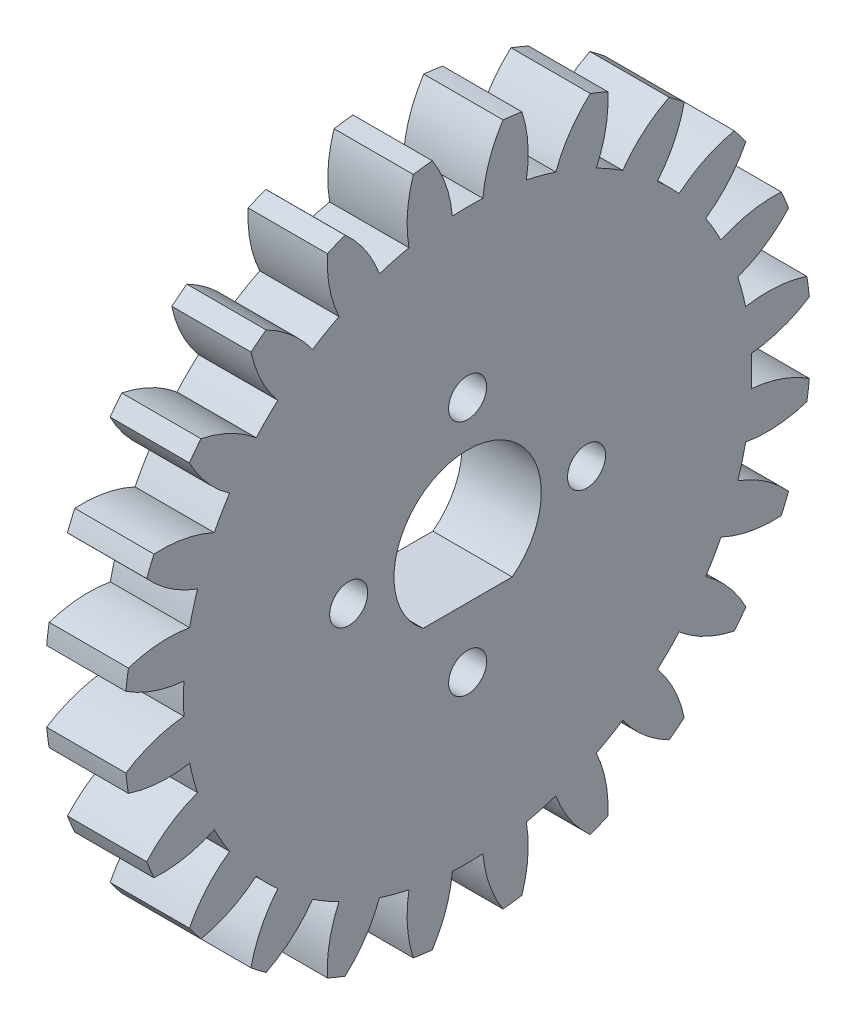
SolidWorks part; units mm, degrees
ref_plane "Plane1" through (0, 0, 0) normal (0, 0, 1) x (1, 0, 0)
ref_plane "Plane2" through (0, 0, 0) normal (0, 1, 0) x (1, 0, 0)
ref_plane "Plane3" through (0, 0, 0) normal (1, 0, 0) x (0, 0, -1)
sketch "HoldingSke" plane through (0, 0, 0) normal (0, 1, 0) x (1, 0, 0)
  line L0 (0, 0) -> (556.8973, -247.9467)
  line L1 (-15, 0) -> (100, 0) construction
  line L2 (0, 0) -> (-2.1039, 2.3779)
  line L3 (0, 0) -> (-11.863, 4.5341)
  line L4 (0, 0) -> (7.8894, 3.5126)
  line L5 (0, 0) -> (-47.5972, -17.7524)
  line L6 (0, 0) -> (-2.632, -1.7758)
  line L7 (-2.1039, 2.3779) -> (8.8315, 51.9902)
  line L8 (-76.2, 54.61) -> (-71.1708, 54.61)
  line L9 (-67.7845, 28.3722) -> (-49.3413, 33.142)
  line L10 (-76.2, 71.12) -> (104.1128, 71.12)
  line L11 (0, 0) -> (-3.175, 0)
  line L12 (-76.2, 101.6) -> (-76.1573, 101.6)
  line L13 (24.9733, 27.94) -> (52.9518, 28.4284)
  line L14 (24.9733, 27.94) -> (25.0241, 27.9398)
  line L15 (24.9733, 27.94) -> (100.4021, 29.52)
  circle A0 centre (0, 0) radius 2.3813
  circle A1 centre (0, 0) radius 10.3209
  circle A2 centre (0, 0) radius 38.1
  circle A3 centre (0, 0) radius 2.3813
  dimension "MHD" = 20.6417
  dimension "Hub_dia" = 76.2
  dimension "Bore" = 4.7625
  dimension "MBD" = 4.7625
  dimension "Num_teeth" = 24
  dimension "Pitch_radius" = 180.3128
  dimension "Pitch" = 609.6
  dimension "Width" = 3.175
  dimension "Overall_len" = 50.8
  dimension "Show_teeth" = 24
  dimension "Thickness" = 3.175
  dimension "OAL" = 50.8032
  dimension "T_dim" = 5.0292
  dimension "Ap" = 14.5
  dimension "H" = 19.05
  dimension "Backlash" = 0.0427
  dimension "Addendum_fac" = 1
  dimension "Dedendum_fac" = 1.2
  dimension "Clearance_fac" = 0.2
  dimension "Dedendum_add" = 0.0508
sketch "BasProSke" plane through (0, 0, 0) normal (0, 1, 0) x (1, 0, 0)
  line L0 (-10, 0) -> (60, 0) construction
  line L1 (0, 0) -> (0, 13.7583)
  line L2 (0, 0) -> (3.175, 0)
  line L3 (3.175, 0) -> (3.175, 13.7583)
  line L4 (3.175, 13.7583) -> (0, 13.7583)
  dimension "Diameter" = 27.5167
  dimension "Thickness" = 3.175
revolve "Base-Revolve" add sketch "BasProSke" angle 360 about L0
sketch "TooCutSke" plane through (0, 0, 0) normal (1, 0, 0) x (0, 0, -1)
  line L1 (0, 0) -> (0, 107) construction
  line L2 (0, 0) -> (-0.9053, 12.6677) construction
  line L3 (0, 0) -> (-3.3095, 25.138) construction
  line L4 (-0.9053, 12.6677) -> (-1.6547, 12.569) construction
  arc A0 (0.6115, 11.3628) -> (-0.6115, 11.3628) centre (0, 0) ccw
  arc A1 (1.4324, 13.7091) -> (-1.4324, 13.7091) centre (0, 0) ccw
  circle A2 centre (0, 0) radius 12.7 construction
  circle A3 centre (0, 0) radius 12.2955 construction
  arc A4 (-0.6115, 11.3628) -> (-1.4324, 13.7091) centre (-5.6713, 10.9094) ccw
  arc A5 (1.4324, 13.7091) -> (0.6115, 11.3628) centre (5.6713, 10.9094) ccw
  dimension "Root_dia" = 22.7584
  dimension "Overcut_dia" = 27.5675
  dimension "Pitch_dia" = 25.4
  dimension "Base_dia" = 24.591
  dimension "Flank_rad" = 5.08
  dimension "Half_ang" = 7.5
  dimension "Half_CT" = 0.7559
extrude "ToothCut" cut sketch "TooCutSke" along normal through all
fillet "Breaks" [suppressed] radius 0.0212
fillet "RootFillets" [suppressed] radius 0.2625
pattern_circular "TeethCuts" count 24 every 15 about axis through (-10, 0, 0) along (1, 0, 0) of "ToothCut"
sketch "HubNeaOneSke" plane through (0, 0, 0) normal (-1, 0, 0) x (0, 0, 1)
  circle A0 centre (0, 0) radius 10.3209
  dimension "Diameter" = 20.6417
extrude "HubNearOne" [suppressed] add sketch "HubNeaOneSke" along normal blind 47.6282
sketch "HubNeaBotSke" plane through (0, 0, 0) normal (-1, 0, 0) x (0, 0, 1)
  circle A0 centre (0, 0) radius 10.3209
  dimension "Diameter" = 20.6417
extrude "HubNearBoth" [suppressed] add sketch "HubNeaBotSke" along normal blind 23.8141
ref_plane "FarPln" through (3.175, 0, 0) normal (1, 0, 0) x (0, 0, -1)
sketch "HubFarSke" plane through (3.175, 0, 0) normal (1, 0, 0) x (0, 0, -1)
  circle A0 centre (0, 0) radius 10.3209
  dimension "Diameter" = 20.6417
extrude "HubFar" [suppressed] add sketch "HubFarSke" along normal blind 23.8141
sketch "BorSke" plane through (0, 0, 0) normal (1, 0, 0) x (0, 0, -1)
  circle A0 centre (0, 0) radius 2.3813
  dimension "Diameter" = 4.7625
extrude "Bore" [suppressed] cut sketch "BorSke" along normal mid plane 101.6064
sketch "KeySke" plane through (0, 0, 0) normal (1, 0, 0) x (0, 0, -1)
  line L0 (-0.127, 0) -> (-0.127, 2.6479)
  line L1 (-0.127, 2.6479) -> (0.127, 2.6479)
  line L2 (0.127, 2.6479) -> (0.127, 0)
  line L3 (0, 0) -> (0, 34) construction
  line L4 (-0.127, 0) -> (0.127, 0)
  dimension "Offset" = 2.6479
  dimension "Width" = 0.254
extrude "Keyway" [suppressed] cut sketch "KeySke" along normal mid plane 101.6064
pattern_circular "Keyway2" [suppressed] count 2 every 90 about axis through (-10, 0, 0) along (1, 0, 0)
sketch "Sketch1" plane through (3.175, 0, 0) normal (1, 0, 0) x (0, 0, -1)
  line L0 (-1.7833, -2.35) -> (1.7833, -2.35)
  arc A0 (1.7833, -2.35) -> (-1.7833, -2.35) centre (0, 0) ccw
  dimension "D1" = 5.9
  dimension "D2" = 5.3
extrude "Cut-Extrude1" cut sketch "Sketch1" against normal up to next
sketch "Sketch2" plane through (3.175, 0, 0) normal (1, 0, 0) x (0, 0, -1)
  circle A0 centre (0, 0) radius 12.7
  dimension "D1" = 25.4
sketch "Sketch3" plane through (3.175, 0, 0) normal (1, 0, 0) x (0, 0, -1)
  circle A0 centre (0, 0) radius 4.7625 construction
  circle A1 centre (0, 4.7625) radius 0.762
  circle A2 centre (-4.7625, 0) radius 0.762
  circle A3 centre (4.7625, 0) radius 0.762
  circle A4 centre (0, -4.7625) radius 0.762
  dimension "D1" = 1.524
  dimension "D2" = 9.525
extrude "Cut-Extrude2" cut sketch "Sketch3" against normal up to next
equation "' \"Pitch@HoldingSke\" = 4"
equation "' \"Num_teeth@HoldingSke\" = 12"
equation "' \"Ap@HoldingSke\" =  20"
equation "' \"Width@HoldingSke\" = 0.5"
equation "' \"Hub_dia@HoldingSke\"= 1"
equation "' \"Overall_len@HoldingSke\" = 1.0"
equation "' \"Bore@HoldingSke\" = 0.75"
equation "' \"T_dim@HoldingSke\" = 0.85"
equation "' \"Width@KeySke\" = 0.25"
equation "' \"Show_teeth@HoldingSke\" = 13"
equation "' \"Backlash@HoldingSke\" = 0.009"
equation "' \"Addendum_fac@HoldingSke\" = 1.0"
equation "' \"Dedendum_fac@HoldingSke\" = 1.25"
equation "' \"Dedendum_add@HoldingSke\" = 0.00005"
equation "' \"Clearance_fac@HoldingSke\" = 0.25"
equation "' \"Pitch@HoldingSke\" = 0.5"
equation "' \"Num_teeth@HoldingSke\" =55"
equation "' \"Width@HoldingSke\" = 0.125"
equation "' \"Show_teeth@HoldingSke\" = 23"
equation "' \"Backlash@HoldingSke\" = 0.0375"
equation "\"Overcut_dia@TooCutSke\" = (\"Num_teeth@HoldingSke\" + 2 * \"Addendum_fac@HoldingSke\") / \"Pitch@HoldingSke\" + 0.002"
equation "\"Pitch_dia@TooCutSke\" = \"Num_teeth@HoldingSke\" / \"Pitch@HoldingSke\""
equation "\"Base_dia@TooCutSke\" = \"Num_teeth@HoldingSke\" / \"Pitch@HoldingSke\" * cos((\"Ap@HoldingSke\"  * 3.14159265 / 180))"
equation "\"Root_dia@TooCutSke\" = (\"Num_teeth@HoldingSke\" + 2) / \"Pitch@HoldingSke\" - 2 * (\"Addendum_fac@HoldingSke\" + \"Dedendum_fac@HoldingSke\") / \"Pitch@HoldingSke\" - \"Dedendum_add@HoldingSke\" * 2"
equation "\"Half_ang@TooCutSke\" = 180 / \"Num_teeth@HoldingSke\""
equation "\"Half_CT@TooCutSke\" = \"Num_teeth@HoldingSke\" / \"Pitch@HoldingSke\" * sin((3.14159265 / 2 / \"Num_teeth@HoldingSke\")) / 2 - 7 * \"Backlash@HoldingSke\" / 4"
equation "\"Flank_rad@TooCutSke\" = \"Num_teeth@HoldingSke\" / \"Pitch@HoldingSke\" / 5"
equation "\"Radius@RootFillets\" = \"Clearance_fac@HoldingSke\" / \"Pitch@HoldingSke\" + \"Dedendum_add@HoldingSke\""
equation "\"Break_rad@Breaks\" = 0.02 / \"Pitch@HoldingSke\""
equation "\"Thickness@HoldingSke\" = \"Width@HoldingSke\""
equation "\"OAL@HoldingSke\" = \"Thickness@HoldingSke\""
equation "\"MHD@HoldingSke\" = (\"Num_teeth@HoldingSke\" + 2) / \"Pitch@HoldingSke\" - 2 * (\"Addendum_fac@HoldingSke\" + \"Dedendum_fac@HoldingSke\")  / \"Pitch@HoldingSke\" - \"Dedendum_add@HoldingSke\" * 2"
equation "\"MBD@HoldingSke\" = (\"Num_teeth@HoldingSke\" + 2) / \"Pitch@HoldingSke\" - 2 * (\"Addendum_fac@HoldingSke\" + \"Dedendum_fac@HoldingSke\")  / \"Pitch@HoldingSke\" - \"Dedendum_add@HoldingSke\" * 2 - 0.002"
equation "\"MHD@HoldingSke\" = ((sgn( \"MHD@HoldingSke\" - \"Hub_dia@HoldingSke\" )-1)*( \"MHD@HoldingSke\" - \"Hub_dia@HoldingSke\" ))/-2+ \"Hub_dia@HoldingSke\""
equation "\"MBD@HoldingSke\" = ((sgn( \"MBD@HoldingSke\" - \"Bore@HoldingSke\" )-1)*( \"MBD@HoldingSke\" - \"Bore@HoldingSke\" ))/-2+ \"Bore@HoldingSke\""
equation "\"OAL@HoldingSke\" = ((sgn( \"OAL@HoldingSke\" - \"Overall_len@HoldingSke\" )+1)*( \"OAL@HoldingSke\" - \"Overall_len@HoldingSke\" ))/2 + \"Overall_len@HoldingSke\" + 0.000002"
equation "\"Num_teeth@TeethCuts\" = int( \"Show_teeth@HoldingSke\" ) + 1"
equation "\"Num_teeth@TeethCuts\" = ((sgn( \"Num_teeth@TeethCuts\" - \"Num_teeth@HoldingSke\" )-1)*( \"Num_teeth@TeethCuts\" - \"Num_teeth@HoldingSke\" ))/-2+ \"Num_teeth@HoldingSke\""
equation "\"Num_teeth@TeethCuts\" = ((sgn( \"Num_teeth@TeethCuts\" - 2.0)+1)*( \"Num_teeth@TeethCuts\" - 2.0))/2 +2.0"
equation "\"Angle@TeethCuts\" = 360.0 / \"Num_teeth@HoldingSke\""
equation "\"Diameter@BasProSke\" = (\"Num_teeth@HoldingSke\" + 2 * \"Addendum_fac@HoldingSke\") / \"Pitch@HoldingSke\""
equation "\"Thickness@BasProSke\"  = \"Thickness@HoldingSke\""
equation "' \"Fillet_rad@BasProSke\" =  \"Thickness@HoldingSke\" * 0.05"
equation "\"MHD@HoldingSke\" = ((sgn( \"MHD@HoldingSke\" - \"Root_dia@TooCutSke\" )-1)*( \"MHD@HoldingSke\" - \"Root_dia@TooCutSke\" ))/-2+ \"Root_dia@TooCutSke\""
equation "\"Diameter@HubNeaOneSke\" = \"MHD@HoldingSke\""
equation "\"Length@HubNearOne\" = \"OAL@HoldingSke\" - \"Thickness@BasProSke\""
equation "\"Diameter@HubNeaBotSke\" = \"MHD@HoldingSke\""
equation "\"Length@HubNearBoth\" = ( \"OAL@HoldingSke\" - \"Thickness@BasProSke\" ) / 2.0"
equation "\"Thickness@FarPln\" = \"Thickness@BasProSke\""
equation "\"Diameter@HubFarSke\" = \"MHD@HoldingSke\""
equation "\"Length@HubFar\" = ( \"OAL@HoldingSke\" - \"Thickness@BasProSke\" ) / 2.0"
equation "\"Diameter@BorSke\" = \"MBD@HoldingSke\""
equation "\"D1@Bore\" = \"OAL@HoldingSke\" * 2.0"
equation "\"D1@Keyway\" = \"OAL@HoldingSke\" * 2.0"
equation "\"Offset@KeySke\" = \"T_dim@HoldingSke\" - \"MBD@HoldingSke\" / 2.0"
